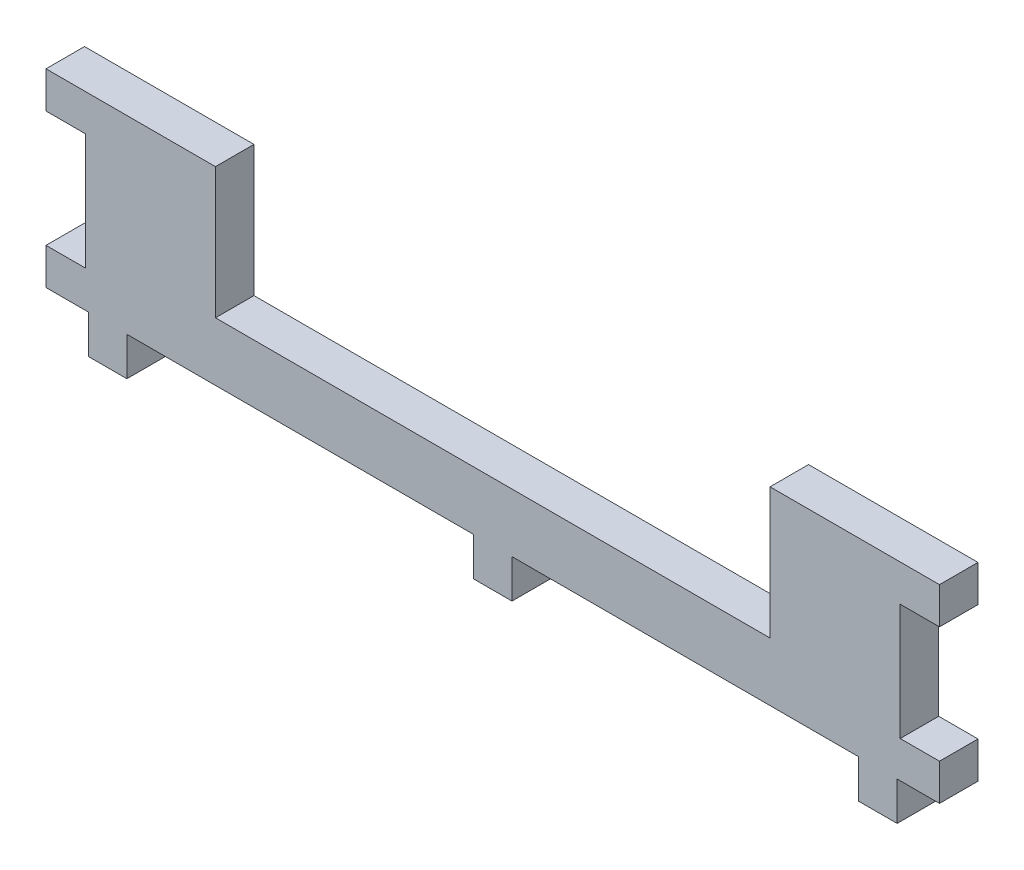
SolidWorks part; units mm, degrees
ref_plane "Front" through (0, 0, 0) normal (0, 0, 1) x (1, 0, 0)
ref_plane "Top" through (0, 0, 0) normal (0, 1, 0) x (1, 0, 0)
ref_plane "Right" through (0, 0, 0) normal (1, 0, 0) x (0, 0, -1)
sketch "Sketch1" plane through (0, 0, 0) normal (0, 0, 1) x (1, 0, 0)
  line L1 (-58, -6.15) -> (58, -6.15)
  line L2 (-58, -6.15) -> (-58, 6.15)
  line L3 (-58, 6.15) -> (58, 6.15)
  line L4 (58, -6.15) -> (58, 6.15)
  line L5 (-58, -6.15) -> (58, 6.15) construction
  line L6 (-58, 6.15) -> (58, -6.15) construction
  point P0 (0, 0)
  dimension "D1" = 12.3
  dimension "D2" = 116
extrude "Boss-Extrude1" add sketch "Sketch1" along normal blind 5
mirror "Mirror1" about plane through (-58, 6.15, 5) normal (0, -1, 0) of bodies 101 102
sketch "Sketch2" plane through (0, -6.15, 0) normal (0, -1, 0) x (1, 0, 0)
  line L0 (-58, 5) -> (58, 5) construction
  line L1 (-52.5, 5) -> (-47.5, 5)
  line L2 (-52.5, 5) -> (-52.5, 0)
  line L3 (-52.5, 0) -> (-47.5, 0)
  line L4 (-47.5, 5) -> (-47.5, 0)
  line L5 (-58, 0) -> (58, 0) construction
  line L6 (-58, 5) -> (-58, 0) construction
  line L11 (47.5, 5) -> (52.5, 5)
  line L12 (47.5, 5) -> (47.5, 0)
  line L13 (47.5, 0) -> (52.5, 0)
  line L14 (52.5, 5) -> (52.5, 0)
  point P16 (-58, 2.5)
  dimension "D1" = 5
  dimension "D3" = 5
  dimension "D5" = 95
  dimension "D6" = 5.5
extrude "Boss-Extrude2" add sketch "Sketch2" along normal blind 5
sketch "Sketch3" plane through (0, 18.45, 0) normal (0, 1, 0) x (1, 0, 0)
  line L0 (-58, 0) -> (58, 0) construction
  line L1 (-36, 0) -> (36, 0)
  line L2 (-36, 0) -> (-36, -5)
  line L3 (-36, -5) -> (36, -5)
  line L4 (36, 0) -> (36, -5)
  line L5 (-58, -5) -> (58, -5) construction
  line L6 (-58, -5) -> (-58, 0) construction
  dimension "D1" = 72
  dimension "D2" = 22
extrude "Cut-Extrude1" cut sketch "Sketch3" against normal blind 17
sketch "Sketch4" plane through (0, -6.15, 0) normal (0, -1, 0) x (1, 0, 0)
  line L0 (-47.5, 5) -> (47.5, 5) construction
  line L1 (-2.5, 5) -> (2.5, 5)
  line L2 (-2.5, 5) -> (-2.5, 0)
  line L3 (-2.5, 0) -> (2.5, 0)
  line L4 (2.5, 5) -> (2.5, 0)
  line L5 (-47.5, 0) -> (47.5, 0) construction
  line L6 (-47.5, 0) -> (-47.5, 5) construction
  dimension "D1" = 5
  dimension "D2" = 45
extrude "Boss-Extrude3" add sketch "Sketch4" along normal blind 5
sketch "Sketch5" plane through (-58, 0, 0) normal (-1, 0, 0) x (0, 0, 1)
  line L0 (0, 18.45) -> (0, -6.15) construction
  line L1 (0, 13.7) -> (5, 13.7)
  line L2 (0, 13.7) -> (0, -1.4)
  line L3 (0, -1.4) -> (5, -1.4)
  line L4 (5, 13.7) -> (5, -1.4)
  line L5 (5, 18.45) -> (5, -6.15) construction
  line L7 (5, -11.15) -> (0, -11.15) construction
  dimension "D1" = 15.1
  dimension "D2" = 9.75
extrude "Cut-Extrude2" cut sketch "Sketch5" against normal blind 5.1
mirror "Mirror2" about plane through (0, 0, 0) normal (1, 0, 0) of "Cut-Extrude2"
